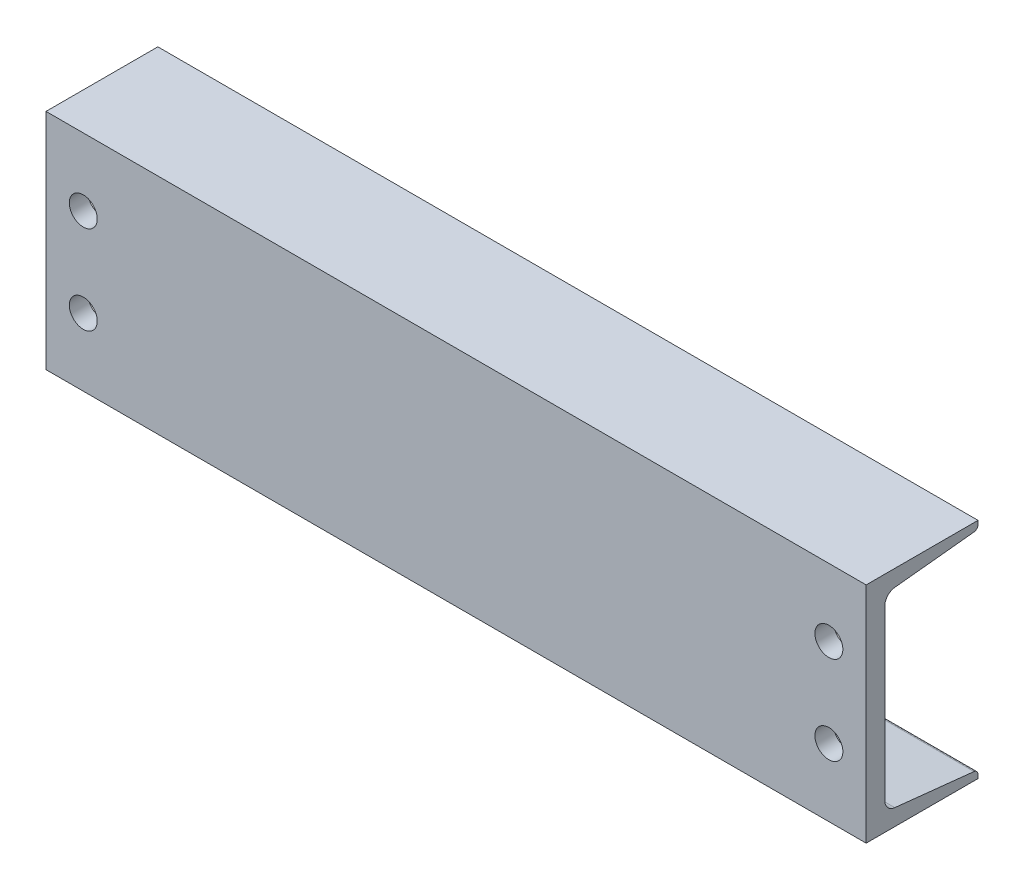
SolidWorks part; units mm, degrees
ref_plane "Front Plane" through (0, 0, 0) normal (0, 0, 1) x (1, 0, 0)
ref_plane "Top Plane" through (0, 0, 0) normal (0, 1, 0) x (1, 0, 0)
ref_plane "Right Plane" through (0, 0, 0) normal (1, 0, 0) x (0, 0, -1)
sketch "Sketch1" plane through (0, 0, 0) normal (1, 0, 0) x (0, 0, -1)
  line L0 (-48.8061, -76.2) -> (-48.8061, 76.2)
  line L1 (-48.8061, 76.2) -> (27.3939, 76.2)
  line L2 (-48.8061, -76.2) -> (27.3939, -76.2)
  line L3 (4.3561, -67.4878) -> (-21.0439, -67.4878) construction
  line L4 (-36.1061, 57.3918) -> (-36.1061, -57.3918)
  line L5 (27.3939, 76.2) -> (27.3939, 73.7107)
  line L6 (27.3939, -76.2) -> (27.3939, -73.7107)
  line L7 (-29.2881, 64.9695) -> (24.6667, 70.6797)
  line L8 (-29.2881, -64.9695) -> (24.6667, -70.6797)
  arc A0 (-36.1061, -57.3918) -> (-29.2881, -64.9695) centre (-28.4861, -57.3918) ccw
  arc A1 (-36.1061, 57.3918) -> (-29.2881, 64.9695) centre (-28.4861, 57.3918) cw
  arc A2 (27.3939, 73.7107) -> (24.6667, 70.6797) centre (24.3459, 73.7107) cw
  arc A3 (27.3939, -73.7107) -> (24.6667, -70.6797) centre (24.3459, -73.7107) ccw
  dimension "D1" = 76.2
  dimension "D2" = 152.4
  dimension "D3" = 12.7
extrude "Boss-Extrude1" add sketch "Sketch1" along normal mid plane 558.8
sketch "Sketch2" plane through (0, 0, 48.8061) normal (0, 0, 1) x (1, 0, 0)
  line L0 (0, 76.2) -> (0, -76.2) construction
  line L1 (279.4, 76.2) -> (-279.4, 76.2) construction
  line L2 (279.4, -76.2) -> (-279.4, -76.2) construction
  line L3 (-279.4, 0) -> (279.4, 0) construction
  line L4 (-279.4, 76.2) -> (-279.4, -76.2) construction
  line L5 (279.4, 76.2) -> (279.4, -76.2) construction
  circle A0 centre (-254, 30.1625) radius 9.525
  circle A1 centre (-254, -30.1625) radius 9.525
  circle A2 centre (254, -30.1625) radius 9.525
  circle A3 centre (254, 30.1625) radius 9.525
  dimension "D1" = 19.05
  dimension "D2" = 46.0375
  dimension "D3" = 25.4
extrude "Cut-Extrude1" cut sketch "Sketch2" against normal up to next
sketch "Sketch3" plane through (0, -76.2, 0) normal (0, -1, 0) x (1, 0, 0)
  line L0 (0, 48.8061) -> (0, -27.3939) construction
  line L1 (279.4, 48.8061) -> (-279.4, 48.8061) construction
  line L2 (279.4, -27.3939) -> (-279.4, -27.3939) construction
  line L3 (-279.4, 48.8061) -> (-279.4, -27.3939) construction
  circle A0 centre (-165.1, 10.7061) radius 9.525
  circle A1 centre (165.1, 10.7061) radius 9.525
  dimension "D3" = 19.05
  dimension "D1" = 38.1
  dimension "D2" = 114.3
extrude "Cut-Extrude2" cut sketch "Sketch3" against normal up to next
